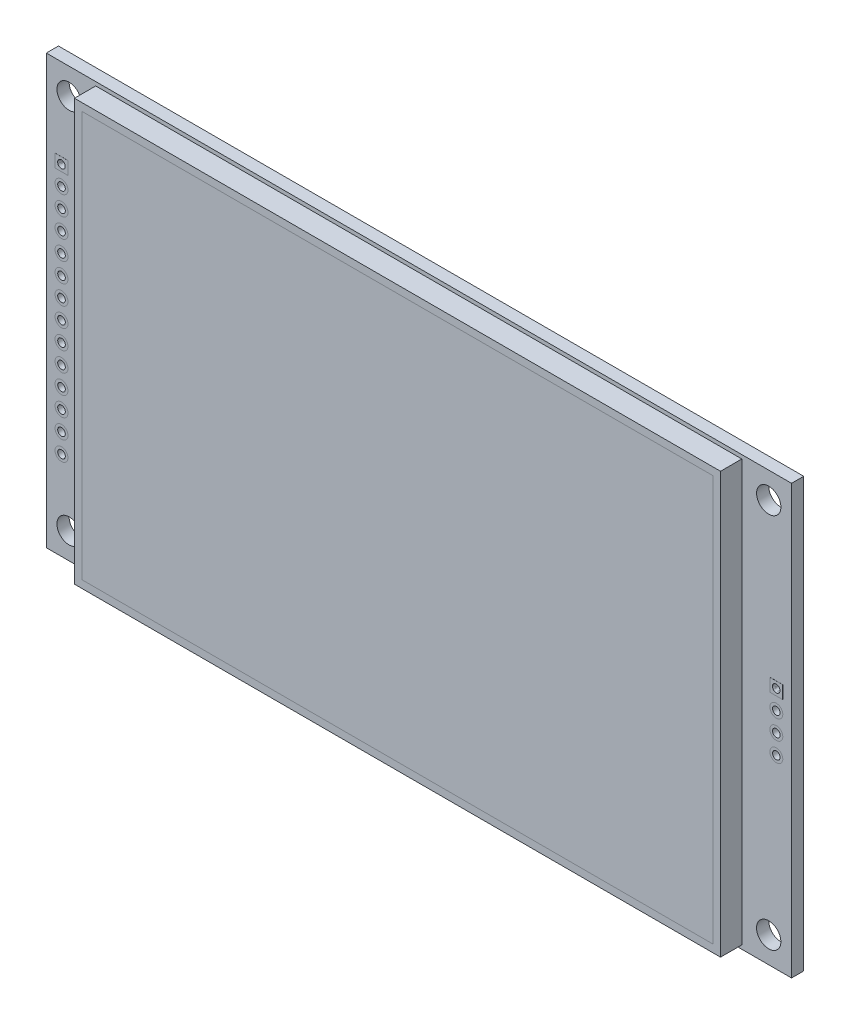
SolidWorks part; units mm, degrees
material "Custom Plastic"
ref_plane "Front Plane" through (0, 0, 0) normal (0, 0, 1) x (1, 0, 0)
ref_plane "Top Plane" through (0, 0, 0) normal (0, 1, 0) x (1, 0, 0)
ref_plane "Right Plane" through (0, 0, 0) normal (1, 0, 0) x (0, 0, -1)
sketch "Sketch2" plane through (0, 0, 0) normal (0, 0, 1) x (1, 0, 0)
  line L1 (-49, 28.17) -> (49, 28.17)
  line L2 (-49, 28.17) -> (-49, -28.17)
  line L3 (-49, -28.17) -> (49, -28.17)
  line L4 (49, 28.17) -> (49, -28.17)
  line L5 (-49, 28.17) -> (49, -28.17) construction
  line L6 (-49, -28.17) -> (49, 28.17) construction
  point P0 (0, 0)
  dimension "D1" = 98
  dimension "D2" = 56.34
extrude "Boss-Extrude1" add sketch "Sketch2" against normal mid plane 1.6
sketch "Sketch3" plane through (0, 0, 0.8) normal (0, 0, 1) x (1, 0, 0)
  line L0 (-49, 28.17) -> (-49, -28.17) construction
  line L1 (49, 28.17) -> (-49, 28.17) construction
  circle A0 centre (-46, 24.75) radius 1.6
  dimension "D1" = 3.2
  dimension "D2" = 3
  dimension "D3" = 3.42
extrude "Cut-Extrude1" cut sketch "Sketch3" against normal through all
mirror "Mirror1" about plane through (0, 0, 0) normal (1, 0, 0) of "Cut-Extrude1"
mirror "Mirror2" about plane through (0, 0, 0) normal (0, 1, 0) of "Mirror1", "Cut-Extrude1"
sketch "Sketch5" plane through (0, 0, 0.8) normal (0, 0, 1) x (1, 0, 0)
  line L1 (-42.5, 27.67) -> (42.46, 27.67)
  line L2 (-42.5, 27.67) -> (-42.5, -27.67)
  line L3 (-42.5, -27.67) -> (42.46, -27.67)
  line L4 (42.46, 27.67) -> (42.46, -27.67)
  line L5 (-49, 28.17) -> (-49, -28.17) construction
  line L6 (-49, -28.17) -> (49, -28.17) construction
  line L8 (-41.5, -26.67) -> (41.46, -26.67)
  line L9 (-41.5, -26.67) -> (-41.5, 26.67)
  line L10 (-41.5, 26.67) -> (41.46, 26.67)
  line L11 (41.46, -26.67) -> (41.46, 26.67)
  dimension "D1" = 55.34
  dimension "D2" = 84.96
  dimension "D3" = 6.5
  dimension "D4" = 0.5
  dimension "D5" = 1
  dimension "D6" = 1
  dimension "D7" = 1
  dimension "D8" = 1
extrude "Boss-Extrude2" add sketch "Sketch5" along normal blind 2.8
sketch "Sketch6" plane through (0, 0, 0.8) normal (0, 0, 1) x (1, 0, 0)
  line L0 (-41.5, 26.67) -> (-41.5, -26.67) construction
  line L1 (41.46, -26.67) -> (-41.5, -26.67)
  line L2 (41.46, -26.67) -> (41.46, 26.67)
  line L3 (41.46, 26.67) -> (-41.5, 26.67)
  line L4 (-41.5, -26.67) -> (-41.5, 26.67)
  line L5 (41.46, 26.67) -> (-41.5, 26.67) construction
  dimension "D1" = 0
extrude "Boss-Extrude3" add sketch "Sketch6" along normal blind 2.8 separate body
sketch "Sketch9" plane through (0, 0, 0.8) normal (0, 0, 1) x (1, 0, 0)
  line L1 (-46, 24.75) -> (-46, -24.75) construction
  line L2 (-49, 28.17) -> (-49, -28.17) construction
  line L3 (49, 28.17) -> (-49, 28.17) construction
  circle A0 centre (-47, 16.51) radius 0.85
  circle A1 centre (-47, 13.97) radius 0.85
  circle A2 centre (-47, 11.43) radius 0.85
  circle A3 centre (-47, 8.89) radius 0.85
  circle A4 centre (-47, 6.35) radius 0.85
  circle A5 centre (-47, 3.81) radius 0.85
  circle A6 centre (-47, 1.27) radius 0.85
  circle A7 centre (-47, -1.27) radius 0.85
  circle A8 centre (-47, -3.81) radius 0.85
  circle A9 centre (-47, -6.35) radius 0.85
  circle A10 centre (-47, -8.89) radius 0.85
  circle A11 centre (-47, -11.43) radius 0.85
  circle A12 centre (-47, -13.97) radius 0.85
  circle A13 centre (-47, -16.51) radius 0.85
  dimension "D1" = 1.7
  dimension "D2" = 2
  dimension "D3" = 11.66
  dimension "D4" = 14
extrude "Cut-Extrude2" cut sketch "Sketch9" against normal through all
sketch "Sketch10" plane through (0, 0, 0.8) normal (0, 0, 1) x (1, 0, 0)
  circle A0 centre (-47, 16.51) radius 0.85
  circle A1 centre (-47, 16.51) radius 0.5
  circle A2 centre (-47, 13.97) radius 0.5
  circle A3 centre (-47, 13.97) radius 0.85
  circle A4 centre (-47, 11.43) radius 0.5
  circle A5 centre (-47, 11.43) radius 0.85
  circle A6 centre (-47, 8.89) radius 0.5
  circle A7 centre (-47, 8.89) radius 0.85
  circle A8 centre (-47, 6.35) radius 0.5
  circle A9 centre (-47, 6.35) radius 0.85
  circle A10 centre (-47, 3.81) radius 0.5
  circle A11 centre (-47, 3.81) radius 0.85
  circle A12 centre (-47, 1.27) radius 0.5
  circle A13 centre (-47, 1.27) radius 0.85
  circle A14 centre (-47, -1.27) radius 0.5
  circle A15 centre (-47, -1.27) radius 0.85
  circle A16 centre (-47, -3.81) radius 0.5
  circle A17 centre (-47, -3.81) radius 0.85
  circle A18 centre (-47, -6.35) radius 0.5
  circle A19 centre (-47, -6.35) radius 0.85
  circle A20 centre (-47, -8.89) radius 0.5
  circle A21 centre (-47, -8.89) radius 0.85
  circle A22 centre (-47, -11.43) radius 0.5
  circle A23 centre (-47, -11.43) radius 0.85
  circle A24 centre (-47, -13.97) radius 0.5
  circle A25 centre (-47, -13.97) radius 0.85
  circle A26 centre (-47, -16.51) radius 0.5
  circle A27 centre (-47, -16.51) radius 0.85
  dimension "D1" = 1
  dimension "D2" = 1.7
  dimension "D3" = 14
extrude "Boss-Extrude4" add sketch "Sketch10" against normal up to surface (1.6 mm away) separate body up to face at (-46.15, 16.51, -0.8)
sketch "Sketch11" plane through (0, 0, 0.8) normal (0, 0, 1) x (1, 0, 0)
  line L0 (49, -28.17) -> (49, 28.17) construction
  line L1 (49, 28.17) -> (-49, 28.17) construction
  circle A0 centre (47, 3.81) radius 0.85
  circle A1 centre (47, 1.27) radius 0.85
  circle A2 centre (47, -1.27) radius 0.85
  circle A3 centre (47, -3.81) radius 0.85
  dimension "D1" = 1.7
  dimension "D2" = 2
  dimension "D3" = 24.36
  dimension "D4" = 4
extrude "Cut-Extrude3" cut sketch "Sketch11" against normal through all
sketch "Sketch12" plane through (0, 0, 0.8) normal (0, 0, 1) x (1, 0, 0)
  circle A0 centre (47, 3.81) radius 0.85
  circle A1 centre (47, 3.81) radius 0.5
  circle A2 centre (47, 1.27) radius 0.85
  circle A3 centre (47, 1.27) radius 0.5
  circle A4 centre (47, -1.27) radius 0.85
  circle A5 centre (47, -1.27) radius 0.5
  circle A6 centre (47, -3.81) radius 0.85
  circle A7 centre (47, -3.81) radius 0.5
  dimension "D1" = 1.7
  dimension "D2" = 1
  dimension "D3" = 4
extrude "Boss-Extrude5" add sketch "Sketch12" against normal up to surface (1.6 mm away) separate body up to face at (47.85, 3.81, -0.8)
sketch "Sketch13" plane through (0, 0, 0.8) normal (0, 0, 1) x (1, 0, 0)
  line L1 (-47.85, 17.36) -> (-46.15, 17.36)
  line L2 (-47.85, 17.36) -> (-47.85, 15.66)
  line L3 (-47.85, 15.66) -> (-46.15, 15.66)
  line L4 (-46.15, 17.36) -> (-46.15, 15.66)
  line L5 (-47.85, 17.36) -> (-46.15, 15.66) construction
  line L6 (-47.85, 15.66) -> (-46.15, 17.36) construction
  circle A0 centre (-47, 16.51) radius 0.5
  dimension "D1" = 1.7
  dimension "D2" = 1.7
extrude "Boss-Extrude7" add sketch "Sketch13" against normal mid plane 1.62 from offset 0.8 separate body offset against normal yes
sketch "Sketch15" plane through (0, 0, 0.8) normal (0, 0, 1) x (1, 0, 0)
  line L1 (46.15, 4.66) -> (47.85, 4.66)
  line L2 (46.15, 4.66) -> (46.15, 2.96)
  line L3 (46.15, 2.96) -> (47.85, 2.96)
  line L4 (47.85, 4.66) -> (47.85, 2.96)
  line L5 (46.15, 4.66) -> (47.85, 2.96) construction
  line L6 (46.15, 2.96) -> (47.85, 4.66) construction
  circle A0 centre (47, 3.81) radius 0.5
  dimension "D3" = 1
  dimension "D1" = 1.7
  dimension "D2" = 1.7
extrude "Boss-Extrude8" add sketch "Sketch15" along normal mid plane 1.62 from offset 0.8 separate body
